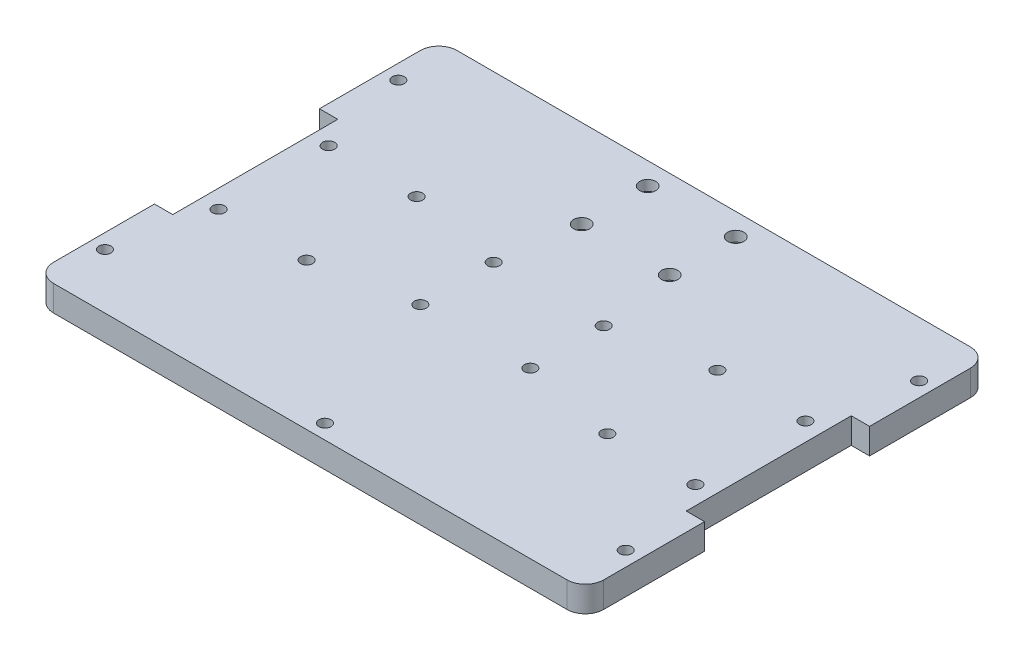
SolidWorks part; units mm, degrees
ref_plane "前视基准面" through (0, 0, 0) normal (0, 0, 1) x (1, 0, 0)
ref_plane "上视基准面" through (0, 0, 0) normal (0, 1, 0) x (1, 0, 0)
ref_plane "右视基准面" through (0, 0, 0) normal (1, 0, 0) x (0, 0, -1)
sketch "草图1" plane through (0, 0, 0) normal (0, 1, 0) x (1, 0, 0)
  line L1 (-75, 55) -> (75, 55)
  line L2 (-75, 55) -> (-75, -55)
  line L3 (-75, -55) -> (75, -55)
  line L4 (75, 55) -> (75, -55)
  line L5 (-75, 55) -> (75, -55) construction
  line L6 (-75, -55) -> (75, 55) construction
  point P0 (0, 0)
  dimension "D1" = 150
  dimension "D2" = 110
extrude "凸台-拉伸1" add sketch "草图1" along normal blind 7
fillet "圆角1" radius 5 4 edges at (-75, 3.5, -55) (75, 3.5, -55) (75, 3.5, 55) (-75, 3.5, 55)
sketch "草图2" plane through (0, 7, 0) normal (0, 1, 0) x (1, 0, 0)
  line L0 (0, 0) -> (0, 57.5872) construction
  line L1 (75, -50) -> (75, 50) construction
  line L2 (65, -15) -> (41, -15) construction
  line L3 (65, -15) -> (65, 15) construction
  line L4 (65, 15) -> (41, 15) construction
  line L5 (41, -15) -> (41, 15) construction
  line L6 (65, -15) -> (41, 15) construction
  line L7 (65, 15) -> (41, -15) construction
  line L8 (-65, 15) -> (-41, -15) construction
  line L9 (-65, -15) -> (-41, 15) construction
  line L10 (-41, -15) -> (-41, 15) construction
  line L11 (-65, 15) -> (-41, 15) construction
  line L12 (-65, -15) -> (-65, 15) construction
  line L13 (-65, -15) -> (-41, -15) construction
  line L14 (70, 55) -> (-70, 55) construction
  line L15 (12, 31) -> (-12, 31) construction
  line L16 (12, 31) -> (12, 49) construction
  line L17 (12, 49) -> (-12, 49) construction
  line L18 (-12, 31) -> (-12, 49) construction
  line L19 (12, 31) -> (-12, 49) construction
  line L20 (12, 49) -> (-12, 31) construction
  line L21 (0, 0) -> (0, -59.6522) construction
  line L23 (15, 10) -> (-15, 10) construction
  line L24 (15, 10) -> (15, -10) construction
  line L25 (15, -10) -> (-15, -10) construction
  line L26 (-15, 10) -> (-15, -10) construction
  line L27 (15, 10) -> (-15, -10) construction
  line L28 (15, -10) -> (-15, 10) construction
  circle A0 centre (65, -15) radius 1.65
  circle A1 centre (41, -15) radius 1.65
  circle A2 centre (41, 15) radius 1.65
  circle A3 centre (65, 15) radius 1.65
  circle A4 centre (-65, 15) radius 1.65
  circle A5 centre (-41, 15) radius 1.65
  circle A6 centre (-41, -15) radius 1.65
  circle A7 centre (-65, -15) radius 1.65
  circle A8 centre (12, 31) radius 2.2
  circle A9 centre (12, 49) radius 2.2
  circle A10 centre (-12, 49) radius 2.2
  circle A11 centre (-12, 31) radius 2.2
  circle A12 centre (15, 10) radius 1.65
  circle A13 centre (15, -10) radius 1.65
  circle A14 centre (-15, -10) radius 1.65
  circle A15 centre (-15, 10) radius 1.65
  point P3 (53, 0)
  point P22 (-53, 0)
  point P23 (0, 40)
  dimension "D4" = 3.3
  dimension "D5" = 3.3
  dimension "D6" = 3.3
  dimension "D7" = 3.3
  dimension "D11" = 4.4
  dimension "D12" = 4.4
  dimension "D15" = 3.3
  dimension "D16" = 3.3
  dimension "D1" = 24
  dimension "D2" = 30
  dimension "D3" = 10
  dimension "D8" = 24
  dimension "D9" = 18
  dimension "D10" = 6
  dimension "D13" = 30
  dimension "D14" = 20
extrude "切除-拉伸1" cut sketch "草图2" against normal through all
sketch "草图3" plane through (0, 7, 0) normal (0, 1, 0) x (1, 0, 0)
  line L0 (-70, -55) -> (70, -55) construction
  line L5 (25, 0) -> (-25, 0)
  line L6 (25, 0) -> (25, -55)
  line L7 (25, -55) -> (-25, -55)
  line L8 (-25, 0) -> (-25, -55)
  line L9 (25, 0) -> (-25, -55) construction
  line L10 (25, -55) -> (-25, 0) construction
  point P0 (0, -27.5)
  dimension "D1" = 55
  dimension "D2" = 50
sketch "草图5" plane through (0, 0, 0) normal (0, -1, 0) x (1, 0, 0)
  line L0 (0, 0) -> (0, -84.0848) construction
  circle A0 centre (12, -49) radius 3.75
  circle A1 centre (12, -31) radius 3.75
  circle A2 centre (-12, -31) radius 3.75
  circle A3 centre (-12, -49) radius 3.75
  dimension "D1" = 7.5
  dimension "D2" = 7.5
extrude "切除-拉伸3" cut sketch "草图5" against normal blind 4.2
sketch "草图6" plane through (0, 0, 0) normal (0, -1, 0) x (1, 0, 0)
  line L0 (0, 0) -> (0, -78.2556) construction
  line L1 (-39.3257, 17.9) -> (-37.6514, 15)
  line L2 (61.6514, -15) -> (63.3257, -17.9)
  line L3 (63.3257, -17.9) -> (66.6743, -17.9)
  line L4 (66.6743, -17.9) -> (68.3486, -15)
  line L5 (68.3486, -15) -> (66.6743, -12.1)
  line L6 (66.6743, -12.1) -> (63.3257, -12.1)
  line L7 (63.3257, -12.1) -> (61.6514, -15)
  line L8 (37.6514, -15) -> (39.3257, -17.9)
  line L9 (39.3257, -17.9) -> (42.6743, -17.9)
  line L10 (42.6743, -17.9) -> (44.3486, -15)
  line L11 (44.3486, -15) -> (42.6743, -12.1)
  line L12 (42.6743, -12.1) -> (39.3257, -12.1)
  line L13 (39.3257, -12.1) -> (37.6514, -15)
  line L14 (61.6514, 15) -> (63.3257, 12.1)
  line L15 (63.3257, 12.1) -> (66.6743, 12.1)
  line L16 (66.6743, 12.1) -> (68.3486, 15)
  line L17 (68.3486, 15) -> (66.6743, 17.9)
  line L18 (66.6743, 17.9) -> (63.3257, 17.9)
  line L19 (63.3257, 17.9) -> (61.6514, 15)
  line L20 (37.6514, 15) -> (39.3257, 12.1)
  line L21 (39.3257, 12.1) -> (42.6743, 12.1)
  line L22 (42.6743, 12.1) -> (44.3486, 15)
  line L23 (44.3486, 15) -> (42.6743, 17.9)
  line L24 (42.6743, 17.9) -> (39.3257, 17.9)
  line L25 (39.3257, 17.9) -> (37.6514, 15)
  line L26 (-42.6743, 17.9) -> (-39.3257, 17.9)
  line L27 (-44.3486, 15) -> (-42.6743, 17.9)
  line L28 (-42.6743, 12.1) -> (-44.3486, 15)
  line L29 (-39.3257, 12.1) -> (-42.6743, 12.1)
  line L30 (-37.6514, 15) -> (-39.3257, 12.1)
  line L31 (-63.3257, 17.9) -> (-61.6514, 15)
  line L32 (-66.6743, 17.9) -> (-63.3257, 17.9)
  line L33 (-68.3486, 15) -> (-66.6743, 17.9)
  line L34 (-66.6743, 12.1) -> (-68.3486, 15)
  line L35 (-63.3257, 12.1) -> (-66.6743, 12.1)
  line L36 (-61.6514, 15) -> (-63.3257, 12.1)
  line L37 (-39.3257, -12.1) -> (-37.6514, -15)
  line L38 (-42.6743, -12.1) -> (-39.3257, -12.1)
  line L39 (-44.3486, -15) -> (-42.6743, -12.1)
  line L40 (-42.6743, -17.9) -> (-44.3486, -15)
  line L41 (-39.3257, -17.9) -> (-42.6743, -17.9)
  line L42 (-37.6514, -15) -> (-39.3257, -17.9)
  line L43 (-63.3257, -12.1) -> (-61.6514, -15)
  line L44 (-66.6743, -12.1) -> (-63.3257, -12.1)
  line L45 (-68.3486, -15) -> (-66.6743, -12.1)
  line L46 (-66.6743, -17.9) -> (-68.3486, -15)
  line L47 (-63.3257, -17.9) -> (-66.6743, -17.9)
  line L48 (-61.6514, -15) -> (-63.3257, -17.9)
  circle A0 centre (65, -15) radius 2.9 construction
  circle A1 centre (41, -15) radius 2.9 construction
  circle A2 centre (65, 15) radius 2.9 construction
  circle A3 centre (41, 15) radius 2.9 construction
  circle A4 centre (-41, 15) radius 2.9 construction
  circle A5 centre (-65, 15) radius 2.9 construction
  circle A6 centre (-41, -15) radius 2.9 construction
  circle A7 centre (-65, -15) radius 2.9 construction
  dimension "D1" = 5.8
  dimension "D2" = 5.8
  dimension "D3" = 5.8
  dimension "D4" = 5.8
extrude "切除-拉伸4" cut sketch "草图6" against normal blind 3
sketch "草图7" plane through (0, 0, 0) normal (0, -1, 0) x (1, 0, 0)
  line L0 (0, -64.0114) -> (0, 0) construction
  circle A0 centre (15, -10) radius 2.9
  circle A1 centre (15, 10) radius 2.9
  circle A2 centre (-15, 10) radius 2.9
  circle A3 centre (-15, -10) radius 2.9
  dimension "D1" = 5.8
  dimension "D2" = 5.8
extrude "切除-拉伸5" cut sketch "草图7" against normal blind 3.3
sketch "草图8" plane through (0, 0, 0) normal (0, -1, 0) x (1, 0, 0)
  line L0 (0, 141.0326) -> (0, 0) construction
  line L1 (0, 0) -> (0, -202.0709) construction
  line L2 (0, 0) -> (154.733, 0) construction
  line L3 (75, 50) -> (75, -50) construction
  line L4 (-70, 55) -> (70, 55) construction
  circle A0 centre (71, 40) radius 1.65
  circle A1 centre (71, -40) radius 1.65
  circle A2 centre (-71, -40) radius 1.65
  circle A3 centre (-71, 40) radius 1.65
  circle A4 centre (0, 51) radius 1.65
  dimension "D1" = 3.3
  dimension "D3" = 40
  dimension "D4" = 3.3
  dimension "D5" = 4
  dimension "D2" = 4
extrude "切除-拉伸6" cut sketch "草图8" against normal through all
sketch "草图9" plane through (0, 0, 0) normal (0, -1, 0) x (1, 0, 0)
  circle A0 centre (71, 40) radius 2.9
  circle A1 centre (71, -40) radius 2.9
  circle A2 centre (-71, 40) radius 2.9
  circle A3 centre (-71, -40) radius 2.9
  circle A4 centre (0, 51) radius 2.9
  dimension "D1" = 5.8
  dimension "D2" = 5.8
  dimension "D3" = 5.8
  dimension "D4" = 5.8
  dimension "D5" = 5.8
extrude "切除-拉伸7" cut sketch "草图9" against normal blind 4
sketch "草图10" plane through (0, 7, 0) normal (0, 1, 0) x (1, 0, 0)
  line L0 (0, 0) -> (0, -184.3277) construction
  line L1 (-98.9438, 0) -> (98.9438, 0) construction
  line L2 (75, -50) -> (75, 50) construction
  line L3 (70, 22.5) -> (75, 22.5)
  line L4 (70, 22.5) -> (70, -22.5)
  line L5 (70, -22.5) -> (75, -22.5)
  line L6 (75, 22.5) -> (75, -22.5)
  line L7 (70, 22.5) -> (75, -22.5) construction
  line L8 (70, -22.5) -> (75, 22.5) construction
  line L9 (-70, -22.5) -> (-75, 22.5) construction
  line L10 (-70, 22.5) -> (-75, -22.5) construction
  line L11 (-75, 22.5) -> (-75, -22.5)
  line L12 (-70, -22.5) -> (-75, -22.5)
  line L13 (-70, 22.5) -> (-70, -22.5)
  line L14 (-70, 22.5) -> (-75, 22.5)
  point P3 (72.5, 0)
  point P16 (-72.5, 0)
  dimension "D1" = 5
  dimension "D2" = 45
extrude "切除-拉伸8" cut sketch "草图10" against normal through all
